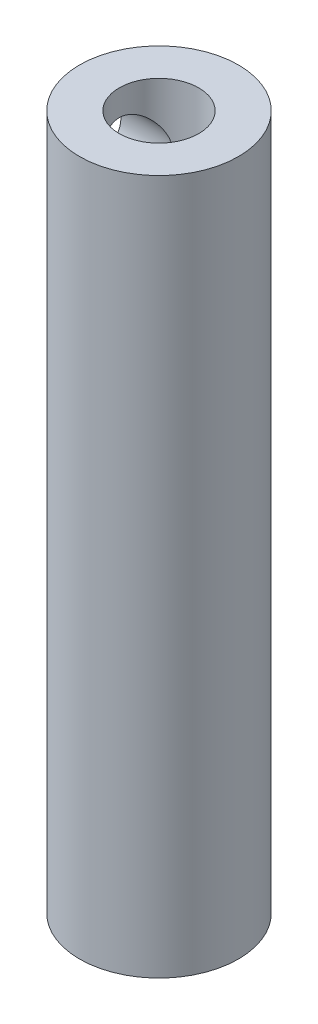
SolidWorks part; units mm, degrees
ref_plane "Alzado" through (0, 0, 0) normal (0, 0, 1) x (1, 0, 0)
ref_plane "Planta" through (0, 0, 0) normal (0, 1, 0) x (1, 0, 0)
ref_plane "Vista lateral" through (0, 0, 0) normal (1, 0, 0) x (0, 0, -1)
sketch "Croquis1" plane through (0, 0, 0) normal (0, 1, 0) x (1, 0, 0)
  circle A0 centre (0, 0) radius 4
  dimension "D1" = 8
extrude "Saliente-Extruir1" add sketch "Croquis1" along normal blind 35
sketch "Croquis2" plane through (0, 35, 0) normal (0, 1, 0) x (1, 0, 0)
  circle A0 centre (0, 0) radius 2
  dimension "D1" = 4
extrude "Cortar-Extruir1" cut sketch "Croquis2" against normal blind 10
hole_wizard "Taladro de margen para M31" positions "Croquis3D2" profile "Croquis3" hole size "M3" standard "Ansi Metric"
sketch3d "Croquis3D2"
  point P0 (-4, 32, 0)
  point P3 (-3.9999, 31.1988, 0.0271)
  dimension "D1" = 32
  dimension "D2" = 0
sketch "Croquis3" plane through (-4, 32, 0) normal (0, 1, 0) x (0, 0, 1)
  line L0 (0, 0) -> (0, 4.0215)
  line L1 (0, 4.0215) -> (1.7, 3)
  line L2 (1.7, 3) -> (1.7, 0)
  line L5 (1.7, 0) -> (0, 0)
  line L10 (0, 4.0215) -> (-1.7, 3) construction
  line L11 (0, -6.35) -> (0, 107.95) construction
  dimension "Diámetro de taladro" = 3.4
  dimension "Profundidad de taladro" = 3
  dimension "Ángulo de perforador" = 118
